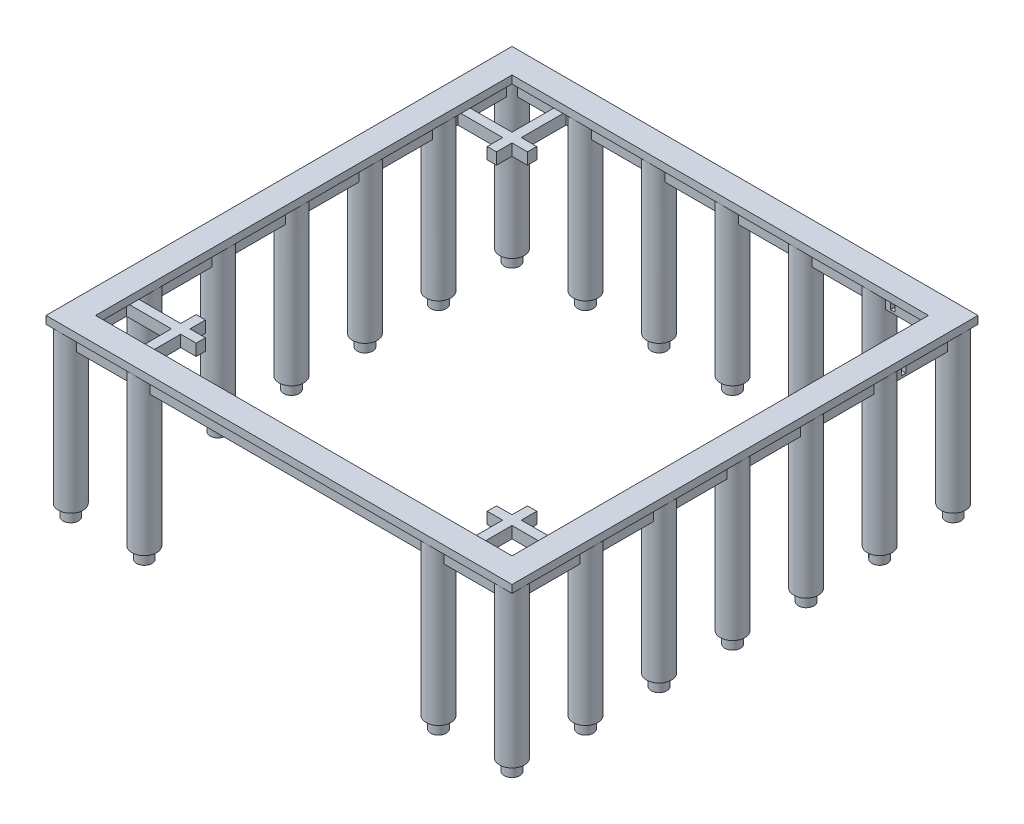
SolidWorks part; units mm, degrees
material "松木"
ref_plane "前视基准面" through (0, 0, 0) normal (0, 0, 1) x (1, 0, 0)
ref_plane "上视基准面" through (0, 0, 0) normal (0, 1, 0) x (1, 0, 0)
ref_plane "右视基准面" through (0, 0, 0) normal (1, 0, 0) x (0, 0, -1)
sketch "草图2" plane through (0, 0, 0) normal (0, 1, 0) x (1, 0, 0)
  line L0 (450, 450) -> (450, 6150)
  line L1 (0, 0) -> (6600, 0)
  line L2 (0, 0) -> (0, 6600)
  line L3 (0, 6600) -> (6600, 6600)
  line L4 (6600, 0) -> (6600, 6600)
  line L5 (450, 6150) -> (6150, 6150)
  line L6 (6150, 450) -> (6150, 6150)
  line L7 (450, 450) -> (6150, 450)
  circle A4 centre (450, 450) radius 160
  circle A5 centre (6150, 450) radius 160
  circle A6 centre (6150, 6150) radius 160
  circle A7 centre (450, 6150) radius 160
  circle A8 centre (450, 5200) radius 160
  circle A9 centre (6150, 5200) radius 160
  circle A10 centre (450, 4250) radius 160
  circle A11 centre (6150, 4250) radius 160
  circle A12 centre (450, 3300) radius 160
  circle A13 centre (6150, 3300) radius 160
  circle A14 centre (450, 2350) radius 160
  circle A15 centre (6150, 2350) radius 160
  circle A16 centre (450, 1400) radius 160
  circle A17 centre (6150, 1400) radius 160
  circle A18 centre (1400, 6150) radius 160
  circle A19 centre (1400, 450) radius 160
  circle A20 centre (2350, 6150) radius 160
  circle A22 centre (3300, 6150) radius 160
  circle A24 centre (4250, 6150) radius 160
  circle A26 centre (5200, 6150) radius 160
  circle A27 centre (5200, 450) radius 160
  circle A28 centre (2350, 450) radius 160 [skipped]
  circle A29 centre (3300, 450) radius 160 [skipped]
  circle A30 centre (4250, 450) radius 160 [skipped]
  dimension "D4" = 320
  dimension "D1" = 6600
  dimension "D2" = 6600
  dimension "D6" = 950
  dimension "D8" = 950
  dimension "D3" = 450
  dimension "D5" = 6
  dimension "D7" = 6
extrude "凸台-拉伸1" add sketch "草图2" along normal blind 2000 contours L7 A5 L6 | L6 A5 L7 | L6 A6 L5 | L5 A6 L6 | L5 A7 L0 | L0 A7 L5 | L0 A4 L7 | L7 A4 L0
sketch "草图4" plane through (0, 2000, 0) normal (0, 1, 0) x (1, 0, 0)
  line L0 (290, 6310) -> (290, 290)
  line L1 (450, 6150) -> (6150, 6150)
  line L2 (450, 6150) -> (450, 450)
  line L3 (450, 450) -> (6150, 450)
  line L4 (6150, 6150) -> (6150, 450)
  line L5 (290, 290) -> (6310, 290)
  line L6 (6310, 6310) -> (6310, 290)
  line L7 (290, 6310) -> (6310, 6310)
  line L8 (610, 5990) -> (610, 610)
  line L9 (610, 610) -> (5990, 610)
  line L10 (5990, 5990) -> (5990, 610)
  line L11 (610, 5990) -> (5990, 5990)
  circle M13 centre (450, 6150) radius 160
  dimension "D1" = 160
  dimension "D2" = 160
extrude "凸台-拉伸2" add sketch "草图4" along normal blind 100 contours L7 L1 L4 L3 L2 L0 L5 L6 M13 | L4 L1 L2 L3 L8 L11 L10 L9 M13 | L2 L1 M13 | L7 L0 M13 | L1 L2 M13
ref_plane "基准面4" through (0, 0, -450) normal (0, 0, 1) x (1, 0, 0)
sketch "草图5" plane through (0, 0, -450) normal (0, 0, 1) x (1, 0, 0)
  line L0 (6150, 1800) -> (6150, 2000)
  line L1 (6310, 2000) -> (5990, 2000)
  line L2 (6310, 2000) -> (6310, 1800)
  line L3 (6310, 1800) -> (5990, 1800)
  line L4 (5990, 2000) -> (5990, 1800)
  line L5 (6150, 2000) -> (6080, 2000)
  line L6 (6080, 2000) -> (6080, 1800)
  line L7 (6220, 2000) -> (6220, 1800)
  dimension "D1" = 320
  dimension "D2" = 200
  dimension "D3" = 70
  dimension "D4" = 70
extrude "凸台-拉伸3" add sketch "草图5" against normal blind 5700 contours L7 L1 L0 L3 | L1 L6 L3 L0
ref_plane "基准面5" through (0, 0, -3300) normal (0, 0, 1) x (1, 0, 0)
ref_plane "基准面6" through (3300, 0, 0) normal (1, 0, 0) x (0, 0, -1)
mirror "镜向3" about plane through (3300, 0, 0) normal (1, 0, 0) of "凸台-拉伸3"
ref_plane "基准面7" through (0, 0, 0) normal (-0.7071, 0, -0.7071) x (-0.7071, 0, 0.7071)
mirror "镜向4" about plane through (0, 0, 0) normal (-0.7071, 0, -0.7071) of "镜向3", "凸台-拉伸3"
sketch "草图9" plane through (0, 0, 0) normal (0, -1, 0) x (1, 0, 0)
  circle A0 centre (6150, -6150) radius 100
  circle A1 centre (5200, -6150) radius 100
  circle A2 centre (4250, -6150) radius 100
  circle A3 centre (3300, -6150) radius 100
  circle A4 centre (2350, -6150) radius 100
  circle A5 centre (1400, -6150) radius 100
  circle A6 centre (450, -6150) radius 100
  circle A7 centre (6150, -5200) radius 100
  circle A8 centre (6150, -4250) radius 100
  circle A9 centre (6150, -3300) radius 100
  circle A10 centre (6150, -2350) radius 100
  circle A11 centre (6150, -1400) radius 100
  circle A12 centre (6150, -450) radius 100
  circle A13 centre (5200, -450) radius 100
  circle A17 centre (1400, -450) radius 100
  circle A18 centre (450, -450) radius 100
  circle A19 centre (450, -5200) radius 100
  circle A20 centre (450, -4250) radius 100
  circle A21 centre (450, -3300) radius 100
  circle A22 centre (450, -2350) radius 100
  circle A23 centre (450, -1400) radius 100
  circle A24 centre (2350, -450) radius 100 [skipped]
  circle A25 centre (3300, -450) radius 100 [skipped]
  circle A26 centre (4250, -450) radius 100 [skipped]
  dimension "D1" = 200
  dimension "D8" = 6
  dimension "D3" = 5700
  dimension "D5" = 5700
  dimension "D7" = 5700
  dimension "D9" = 4750
  dimension "D2" = 7
  dimension "D4" = 7
  dimension "D6" = 7
extrude "凸台-拉伸4" add sketch "草图9" along normal blind 150
sketch "草图11" plane through (0, 2100, 0) normal (0, 1, 0) x (1, 0, 0)
  line L0 (5300, 1300) -> (5300, 5300)
  line L1 (5990, 610) -> (610, 610)
  line L2 (5990, 610) -> (5990, 5990)
  line L3 (5990, 5990) -> (610, 5990)
  line L4 (610, 610) -> (610, 5990)
  line L5 (5300, 5300) -> (1300, 5300)
  line L6 (1300, 1300) -> (1300, 5300)
  line L7 (5300, 1300) -> (1300, 1300)
  line L8 (5500, 1100) -> (5500, 5500)
  line L9 (5500, 5500) -> (1100, 5500)
  line L10 (1100, 1100) -> (1100, 5500)
  line L11 (5500, 1100) -> (1100, 1100)
  line L12 (5300, 1300) -> (5300, 290)
  line L13 (290, 290) -> (6310, 290) construction
  line L14 (5300, 1300) -> (5500, 1300)
  line L15 (5300, 5300) -> (5500, 5300)
  line L16 (5500, 5300) -> (5500, 5500)
  line L17 (5300, 5500) -> (5300, 5300)
  line L18 (1300, 5300) -> (1300, 5500)
  line L19 (1300, 5500) -> (1100, 5500)
  line L20 (1100, 5300) -> (1300, 5300)
  line L21 (1300, 1300) -> (1300, 1100)
  line L22 (1300, 1100) -> (1100, 1100)
  line L23 (1100, 1300) -> (1300, 1300)
  line L24 (1100, 1100) -> (1100, 449.8876)
  line L25 (1100, 449.8876) -> (1300, 449.8876)
  line L26 (1300, 449.8876) -> (1300, 1420)
  line L27 (1300, 1420) -> (1100, 1420)
  line L28 (1100, 1420) -> (1100, 1300)
  line L29 (1220, 1420) -> (1220, 449.8876)
  line L30 (1300, 1300) -> (450, 1300)
  line L31 (450, 1300) -> (450, 1100)
  line L32 (450, 1100) -> (1100, 1100)
  line L33 (450, 1220) -> (1420, 1220)
  line L34 (1420, 1220) -> (1420, 1100)
  dimension "D3" = 200
  dimension "D4" = 200
  dimension "D5" = 120
  dimension "D6" = 650
  dimension "D7" = 120
  dimension "D8" = 200
  dimension "D1" = 690
  dimension "D2" = 200
extrude "凸台-拉伸5" add sketch "草图11" against normal blind 150 from offset 150 contours L33 L31 L32 L4 | L33 L4 L32 L10 | L33 L10 L22 L29 | L33 L29 L11 L26 | L34 L33 L26 L11 | L10 L33 L29 L23 | L29 L27 L10 L23 | L29 L22 L24 L1 | L29 L1 L24 L25 offset against normal yes
mirror "镜向5" about plane through (0, 0, -3300) normal (0, 0, 1) of "凸台-拉伸5"
mirror "镜向6" about plane through (3300, 0, 0) normal (1, 0, 0) of "凸台-拉伸5"
sketch "草图12" plane through (0, 0, -1420) normal (0, 0, -1) x (-1, 0, 0)
  line L0 (-5380, 1800) -> (-5500, 1800) construction
  line L1 (-5470, 1830) -> (-5410, 1830)
  line L2 (-5470, 1830) -> (-5470, 1920)
  line L3 (-5470, 1920) -> (-5410, 1920)
  line L4 (-5410, 1830) -> (-5410, 1920)
  line L5 (-5380, 1950) -> (-5500, 1950) construction
  line L6 (-5500, 1800) -> (-5500, 1950) construction
  dimension "D1" = 30
  dimension "D2" = 30
  dimension "D3" = 60
  dimension "D4" = 30
extrude "切除-拉伸1" cut sketch "草图12" along normal through all
sketch "草图13" plane through (1420, 0, 0) normal (1, 0, 0) x (0, 0, -1)
  line L0 (5380, 1800) -> (5380, 1950) construction
  line L1 (5470, 1830) -> (5410, 1830)
  line L2 (5470, 1830) -> (5470, 1920)
  line L3 (5470, 1920) -> (5410, 1920)
  line L4 (5410, 1830) -> (5410, 1920)
  line L5 (5380, 1950) -> (5500, 1950) construction
  line L6 (5380, 1800) -> (5500, 1800) construction
  line L7 (5500, 1800) -> (5500, 1950) construction
  dimension "D1" = 30
  dimension "D2" = 30
  dimension "D3" = 30
  dimension "D4" = 30
extrude "切除-拉伸2" cut sketch "草图13" along normal through all
